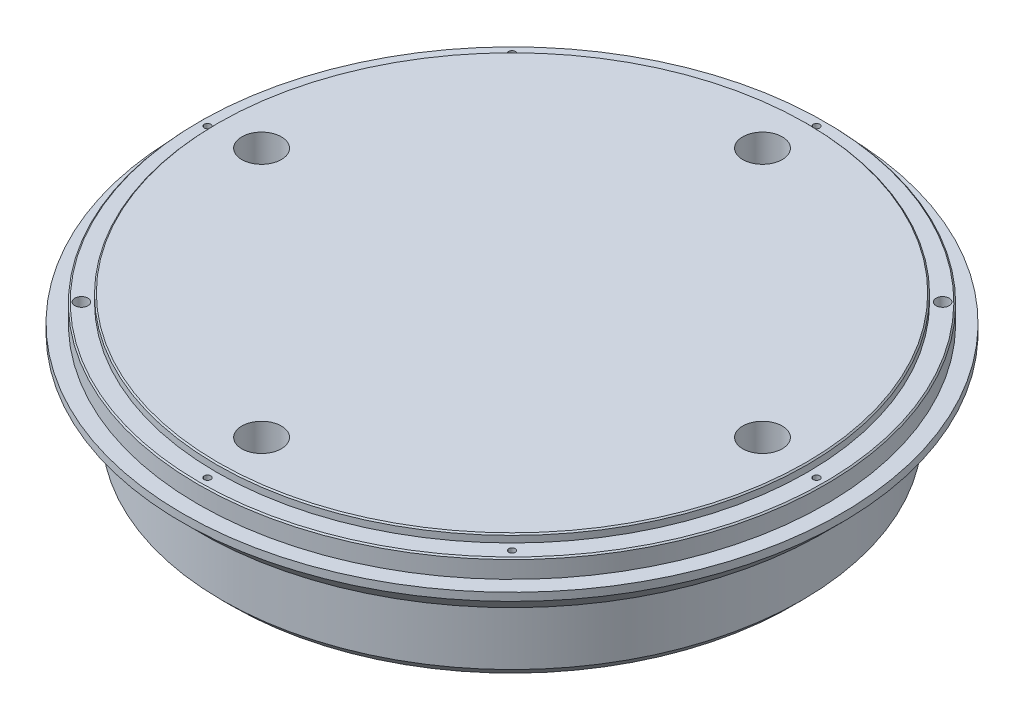
SolidWorks part; units mm, degrees
material "3.3315 (EN-AW 5005)"
ref_plane "Front Plane" through (0, 0, 0) normal (0, 0, 1) x (1, 0, 0)
ref_plane "Top Plane" through (0, 0, 0) normal (0, 1, 0) x (1, 0, 0)
ref_plane "Right Plane" through (0, 0, 0) normal (1, 0, 0) x (0, 0, -1)
sketch "Sketch1" plane through (0, 0, 0) normal (0, 1, 0) x (1, 0, 0)
  circle A0 centre (0, 0) radius 125
  dimension "D1" = 250
extrude "Boss-Extrude1" add sketch "Sketch1" along normal blind 50
sketch "Sketch2" plane through (0, 50, 0) normal (0, 1, 0) x (1, 0, 0)
  circle A0 centre (0, 0) radius 119
  circle A1 centre (0, 0) radius 127
  circle A2 centre (0, 0) radius 125 construction
  dimension "D1" = 254
  dimension "D2" = 6
extrude "Pakning" cut sketch "Sketch2" against normal blind 10
sketch "Sketch3" plane through (0, 50, 0) normal (0, 1, 0) x (1, 0, 0)
  circle A0 centre (0, 0) radius 112
  circle A1 centre (0, 0) radius 125
  circle A2 centre (0, 0) radius 125 construction
  circle A3 centre (0, 0) radius 119 construction
  dimension "D1" = 7
extrude "PakningsRing" cut sketch "Sketch3" against normal blind 3
sketch "Sketch5" plane through (0, 0, 0) normal (0, -1, 0) x (-1, 0, 0)
  line L0 (-42.4264, 42.4264) -> (0, 0) construction
  line L1 (-42.4264, 42.4264) -> (-84.1457, 84.1457) construction
  line L2 (0, 0) -> (0, 67.509) construction
  circle A0 centre (-42.4264, 42.4264) radius 5
  circle A2 centre (0, 0) radius 119 construction
  dimension "D1" = 10
  dimension "D2" = 60
  dimension "D3" = 45
extrude "Varmelement" cut sketch "Sketch5" against normal blind 45
pattern_circular "Varmeelement_pattern" count 4 over 360 about axis through (0, 0, 0) along (0, 1, 0) of "Varmelement"
sketch "Sketch6" plane through (0, 0, 0) normal (0, -1, 0) x (1, 0, 0)
  line L1 (0, 0) -> (14.1421, 14.1421) construction
  line L2 (-42.4264, 42.4264) -> (14.1421, 14.1421) construction
  line L3 (14.1421, 14.1421) -> (42.4264, -42.4264) construction
  circle A0 centre (14.1421, 14.1421) radius 1.5
  dimension "D1" = 3
  dimension "D2" = 20
extrude "Cut-Extrude5" cut sketch "Sketch6" against normal offset from surface (47 mm away) 3 up to face at (0, 50, 112)
sketch "Sketch7" plane through (0, 0, 0) normal (0, -1, 0) x (1, 0, 0)
  circle A0 centre (0, 0) radius 110
  circle A1 centre (0, 0) radius 135
  circle A2 centre (0, 0) radius 125 construction
  dimension "D1" = 10
  dimension "D2" = 220
extrude "Cut-Extrude6" cut sketch "Sketch7" against normal blind 30
chamfer "Chamfer1" distance 7 angle 45 1 edges at (0, 30, -125)
chamfer "Chamfer2" distance 0.5 angle 45 2 edges at (0, 50, 112) (0, 47, 119)
hole_wizard "M12 Tapped Hole1" positions "Sketch10" profile "Sketch9" tap size "M12" standard "ISO"
sketch "Sketch10" plane through (0, 0, 0) normal (0, -1, 0) x (-1, 0, 0)
  point P0 (0, 0)
sketch "Sketch9" plane through (0, 0, 0) normal (1, 0, 0) x (0, 0, -1)
  line L0 (0, 0) -> (0, 23.3144)
  line L1 (0, 23.3144) -> (5.1, 20.25)
  line L2 (5.1, 20.25) -> (5.1, 0)
  line L5 (5.1, 0) -> (0, 0)
  line L10 (0, 23.3144) -> (-5.1, 20.25) construction
  line L11 (0, -6.35) -> (0, 107.95) construction
  dimension "Tap Drill Dia." = 10.2
  dimension "Tap Drill Depth" = 20.25
  dimension "Drill Angle" = 118
cosmetic thread "Hole Thread1" parameters "D1"=15, "D2"=12
sketch "Sketch13" plane through (0, 0, 0) normal (0, -1, 0) x (-1, 0, 0)
  line L0 (0, 0) -> (0, 95) construction
  circle A0 centre (0, 95) radius 8
  dimension "D1" = 16
  dimension "D2" = 95
extrude "Cut-Extrude8" cut sketch "Sketch13" against normal blind 20
hole_wizard "CBORE for M8 Hex Socket Head Cap Screw1" positions "Sketch14" profile "Sketch15" counterbore size "M8" standard "ISO" end condition through all
sketch "Sketch14" plane through (0, 50, 0) normal (0, 1, 0) x (1, 0, 0)
  line L0 (0, 95) -> (0, 0) construction
  circle A0 centre (0, 95) radius 8 construction
  point P0 (0, 95)
sketch "Sketch15" plane through (0, 50, -95) normal (1, 0, 0) x (0, 0, 1)
  line L0 (0, 0) -> (0, 50)
  line L1 (0, 50) -> (4.5, 50)
  line L3 (4.5, 50) -> (4.5, 10.6)
  line L4 (4.5, 10.6) -> (7.5, 10.6)
  line L5 (7.5, 10.6) -> (7.5, 0)
  line L7 (7.5, 0) -> (0, 0)
  line L11 (0, -6.35) -> (0, 107.95) construction
  dimension "Thru Hole Dia." = 9
  dimension "Thru Hole Depth" = 50
  dimension "C'Bore Dia." = 15
  dimension "C'Bore Depth" = 10.6
pattern_circular "CirPattern1" count 4 over 360 about axis through (0, 0, 0) along (0, 1, 0) of "Cut-Extrude8", "CBORE for M8 Hex Socket Head Cap Screw1"
chamfer "Chamfer3" distance 4 angle 45 1 edges at (0, 0, -110)
hole_wizard "M3 Tapped Hole1" positions "Sketch16" profile "Sketch17" tap size "M3" standard "ISO"
sketch "Sketch16" plane through (0, 47, 0) normal (0, 1, 0) x (1, 0, 0)
  line L0 (0, 112) -> (0, 119) construction
  circle A0 centre (0, 0) radius 112 construction
  circle A2 centre (0, 0) radius 119 construction
  point P0 (0, 115.5)
sketch "Sketch17" plane through (0, 47, -115.5) normal (1, 0, 0) x (0, 0, 1)
  line L0 (0, 0) -> (0, 8.2511)
  line L1 (0, 8.2511) -> (1.25, 7.5)
  line L2 (1.25, 7.5) -> (1.25, 0)
  line L5 (1.25, 0) -> (0, 0)
  line L10 (0, 8.2511) -> (-1.25, 7.5) construction
  line L11 (0, -6.35) -> (0, 107.95) construction
  dimension "Tap Drill Dia." = 2.5
  dimension "Tap Drill Depth" = 7.5
  dimension "Drill Angle" = 118
cosmetic thread "Hole Thread2" parameters "D1"=6, "D2"=3
pattern_circular "CirPattern2" count 8 every 45 about axis through (0, 0, 0) along (0, 1, 0) skipping 3, 7 of "M3 Tapped Hole1"
cosmetic thread "Hole Thread3" parameters "D1"=6, "D2"=3
cosmetic thread "Hole Thread4" parameters "D1"=6, "D2"=3
cosmetic thread "Hole Thread5" parameters "D1"=6, "D2"=3
cosmetic thread "Hole Thread6" parameters "D1"=6, "D2"=3
cosmetic thread "Hole Thread7" parameters "D1"=6, "D2"=3
cosmetic thread "Hole Thread8" parameters "D1"=6, "D2"=3
cosmetic thread "Hole Thread9" parameters "D1"=6, "D2"=3
sketch "Sketch18" plane through (0, 47, 0) normal (0, 1, 0) x (1, 0, 0)
  line L0 (95, 0) -> (0, 0) construction
  line L1 (0, 0) -> (0, 95) construction
  line L2 (81.6708, 81.6708) -> (0, 0) construction
  line L3 (0, 95) -> (81.6708, 81.6708) construction
  line L4 (81.6708, 81.6708) -> (95, 0) construction
  circle A0 centre (81.6708, 81.6708) radius 2.5
  circle A1 centre (0, 0) radius 115.5 construction
  dimension "D2" = 5
  dimension "D1" = 45
extrude "Cut-Extrude9" cut sketch "Sketch18" against normal blind 10
pattern_circular "CirPattern3" count 2 over 360 about axis through (0, 0, 0) along (0, 1, 0) of "Cut-Extrude9"
